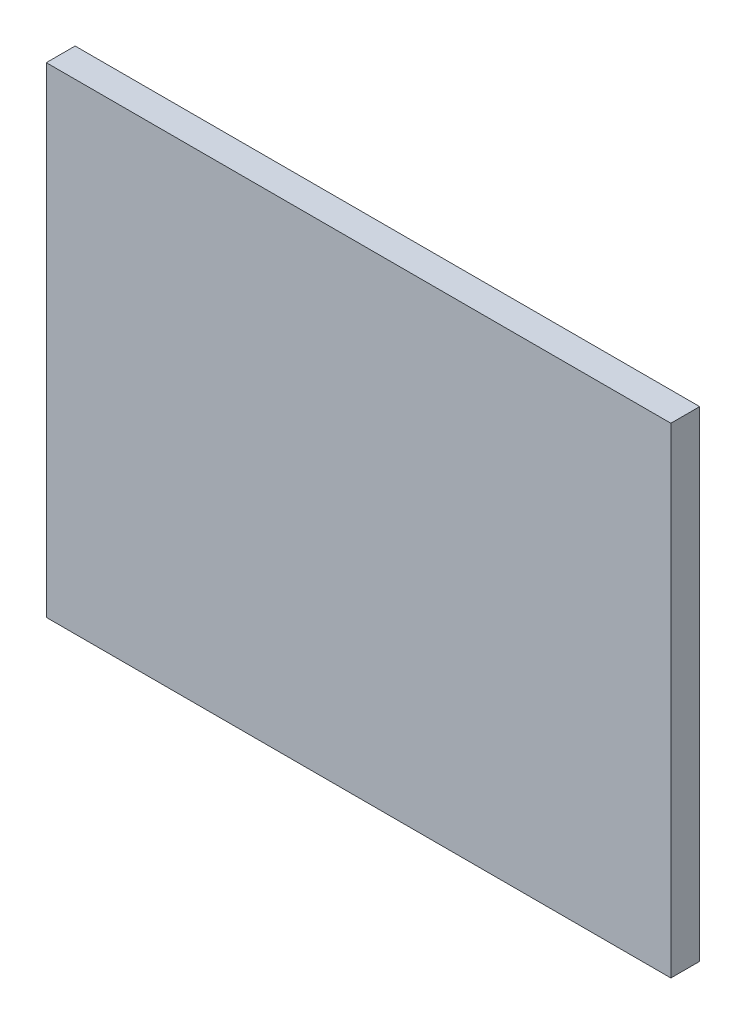
SolidWorks part; units mm, degrees
ref_plane "Front Plane" through (0, 0, 0) normal (0, 0, 1) x (1, 0, 0)
ref_plane "Top Plane" through (0, 0, 0) normal (0, 1, 0) x (1, 0, 0)
ref_plane "Right Plane" through (0, 0, 0) normal (1, 0, 0) x (0, 0, -1)
sketch "Sketch1" plane through (0, 0, 0) normal (0, 0, 1) x (1, 0, 0)
  line L1 (-65, 50) -> (0, 50)
  line L2 (-65, 50) -> (-65, 0)
  line L3 (-65, 0) -> (0, 0)
  line L4 (0, 50) -> (0, 0)
  dimension "D1" = 65
  dimension "D2" = 50
extrude "Boss-Extrude1" add sketch "Sketch1" along normal blind 3
